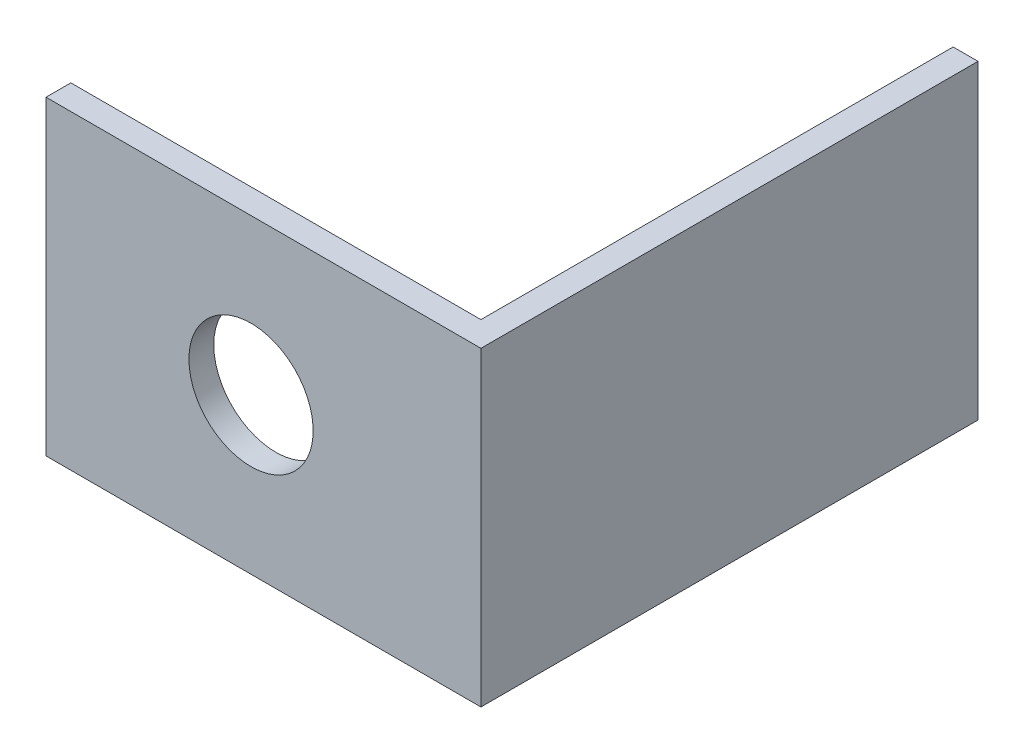
SolidWorks part; units mm, degrees
ref_plane "Front Plane" through (0, 0, 0) normal (0, 0, 1) x (1, 0, 0)
ref_plane "Top Plane" through (0, 0, 0) normal (0, 1, 0) x (1, 0, 0)
ref_plane "Right Plane" through (0, 0, 0) normal (1, 0, 0) x (0, 0, -1)
sketch "Sketch1" plane through (0, 0, 0) normal (0, 1, 0) x (1, 0, 0)
  line L0 (0, 0) -> (44.45, 0)
  line L1 (44.45, 0) -> (44.45, 50.8)
  line L2 (0, 2.54) -> (41.91, 2.54)
  line L3 (41.91, 2.54) -> (41.91, 50.8)
  line L4 (44.45, 50.8) -> (41.91, 50.8)
  line L5 (0, 0) -> (0, 2.54)
  dimension "D1" = 2.54
extrude "Boss-Extrude1" add sketch "Sketch1" along normal blind 31.75
sketch "Sketch2" plane through (0, 0, -2.54) normal (0, 0, -1) x (-1, 0, 0)
  line L0 (0, 15.875) -> (-41.91, 15.875) construction
  line L1 (0, 31.75) -> (0, 0) construction
  line L2 (-41.91, 31.75) -> (-41.91, 0) construction
  circle A0 centre (-20.955, 15.875) radius 6.35
extrude "Cut-Extrude1" cut sketch "Sketch2" against normal blind 31.75
